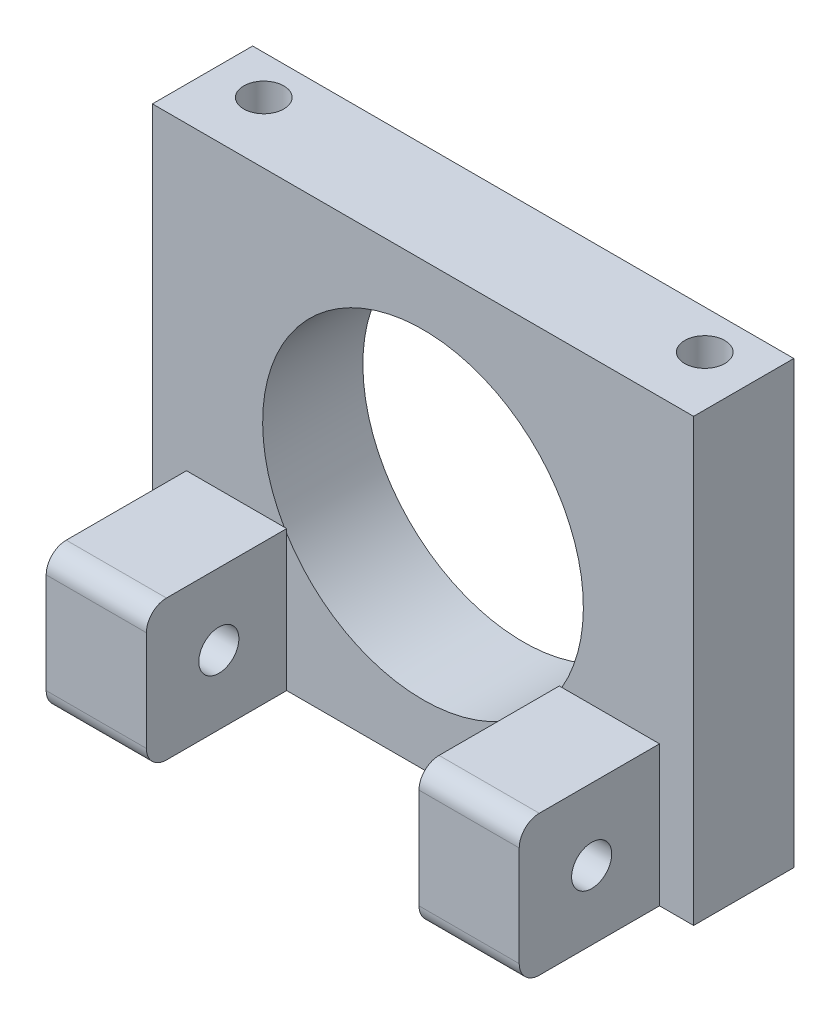
SolidWorks part; units mm, degrees
ref_plane "Front Plane" through (0, 0, 0) normal (0, 0, 1) x (1, 0, 0)
ref_plane "Top Plane" through (0, 0, 0) normal (0, 1, 0) x (1, 0, 0)
ref_plane "Right Plane" through (0, 0, 0) normal (1, 0, 0) x (0, 0, -1)
sketch "Sketch1" plane through (0, 0, 0) normal (0, 0, 1) x (1, 0, 0)
  line L1 (-13.5, 11) -> (13.5, 11)
  line L2 (-13.5, 11) -> (-13.5, -11)
  line L3 (-13.5, -11) -> (13.5, -11)
  line L4 (13.5, 11) -> (13.5, -11)
  line L5 (-13.5, 11) -> (13.5, -11) construction
  line L6 (-13.5, -11) -> (13.5, 11) construction
  circle A0 centre (0, 0) radius 8
  point P0 (0, 0)
  dimension "D1" = 27
  dimension "D2" = 22
extrude "Boss-Extrude1" add sketch "Sketch1" along normal blind 5
sketch "Sketch2" plane through (0, 0, 5) normal (0, 0, 1) x (1, 0, 0)
  line L0 (-13.5, -11) -> (13.5, -11) construction
  line L1 (-11.8, -11) -> (-6.8, -11)
  line L2 (-11.8, -11) -> (-11.8, -4)
  line L3 (-11.8, -4) -> (-6.8, -4)
  line L4 (-6.8, -11) -> (-6.8, -4)
  line L5 (13.5, -11) -> (13.5, 11) construction
  line L6 (6.8, -11) -> (11.8, -11)
  line L7 (6.8, -11) -> (6.8, -4)
  line L8 (6.8, -4) -> (11.8, -4)
  line L9 (11.8, -11) -> (11.8, -4)
  line L10 (-13.5, 11) -> (-13.5, -11) construction
  dimension "D1" = 7
  dimension "D2" = 5
  dimension "D3" = 7
  dimension "D4" = 5
  dimension "1.7" = 1.7
  dimension "D6" = 1.7
extrude "Boss-Extrude2" add sketch "Sketch2" along normal blind 7
sketch "Sketch3" plane through (-11.8, 0, 0) normal (-1, 0, 0) x (0, 0, 1)
  circle A0 centre (8.3862, -7.5614) radius 1
extrude "Cut-Extrude1" cut sketch "Sketch3" against normal through all
fillet "Fillet1" radius 1 4 edges at (9.3, -4, 12) (9.3, -11, 12) (-9.3, -11, 12) (-9.3, -4, 12)
sketch "Sketch4" plane through (0, 11, 0) normal (0, 1, 0) x (1, 0, 0)
  line L0 (-11, -1.9444) -> (11, -1.9444) construction
  line L1 (0, -1.9444) -> (0, 0) construction
  circle A0 centre (-11, -1.9444) radius 1
  circle A1 centre (11, -1.9444) radius 1
  dimension "D2" = 2
  dimension "D3" = 2
  dimension "D1" = 22
extrude "Cut-Extrude2" cut sketch "Sketch4" against normal through all
